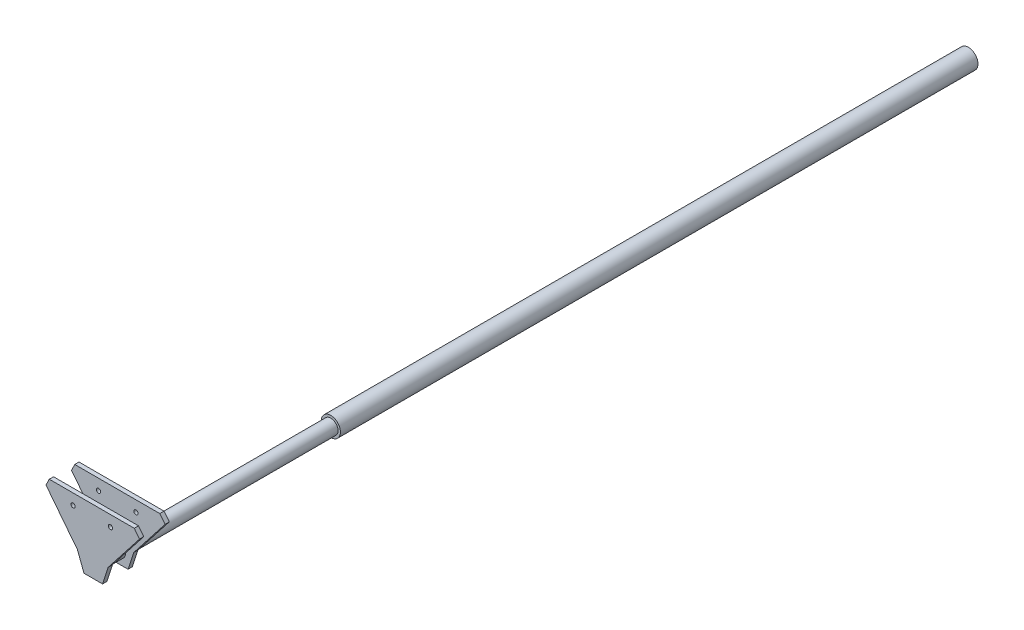
SolidWorks part; units mm, degrees
ref_plane "Front Plane" through (0, 0, 0) normal (0, 0, 1) x (1, 0, 0)
ref_plane "Top Plane" through (0, 0, 0) normal (0, 1, 0) x (1, 0, 0)
ref_plane "Right Plane" through (0, 0, 0) normal (1, 0, 0) x (0, 0, -1)
sketch "Sketch1" plane through (0, 0, 0) normal (0, 0, 1) x (1, 0, 0)
  circle A0 centre (0, 0) radius 11.3
  dimension "D1" = 22.6
extrude "Boss-Extrude1" add sketch "Sketch1" along normal blind 750 from offset 380 offset against normal yes
sketch "Sketch2" plane through (0, 0, 370) normal (0, 0, 1) x (1, 0, 0)
  circle A0 centre (0, 0) radius 8.5
  dimension "D1" = 17
extrude "Boss-Extrude2" add sketch "Sketch2" along normal blind 280
sketch "Sketch3" plane through (0, 0, 650) normal (0, 0, 1) x (1, 0, 0)
  line L0 (0, 20.764) -> (0, -21.3932) construction
  line L1 (11.5212, -14.6879) -> (18.0728, 5.5723)
  line L2 (0, -14.6879) -> (11.5212, -14.6879)
  line L3 (0, -14.6879) -> (-10.3698, -14.6879)
  line L4 (-10.3698, -14.6879) -> (-18.0716, 5.5727)
  line L5 (-18.0716, 5.5727) -> (-55.0272, 52.8409)
  line L6 (18.0728, 5.5723) -> (55.029, 52.84)
  line L7 (-51.1864, 60.7189) -> (48.8136, 60.7189)
  line L10 (-51.1864, 60.7189) -> (-55.0272, 52.8409)
  line L13 (48.8136, 60.7189) -> (55.029, 52.84)
  dimension "D1" = 21.2932
  dimension "D2" = 11.5212
  dimension "D3" = 10.3698
  dimension "D4" = 110.814
  dimension "D5" = 21.6751
  dimension "D6" = 197.206
  dimension "D7" = 100
  dimension "D8" = 107.92
  dimension "D9" = 60
  dimension "D10" = 200.1
extrude "Boss-Extrude3" add sketch "Sketch3" against normal blind 5
pattern_linear "LPattern1" count 2 spacing 30 along (0, 0, -1) of "Boss-Extrude3"
sketch "Sketch6" plane through (0, 0, 650) normal (0, 0, 1) x (1, 0, 0)
  line L0 (-1.1864, 60.7189) -> (-1.1864, 6.6156) construction
  line L1 (48.8136, 60.7189) -> (-51.1864, 60.7189) construction
  circle A0 centre (-23.1865, 47.9373) radius 2.5
  circle A1 centre (20.8136, 47.9373) radius 2.5
  dimension "D3" = 5
  dimension "D1" = 22.0001
  dimension "D2" = 12.7816
extrude "Cut-Extrude1" cut sketch "Sketch6" against normal blind 150
